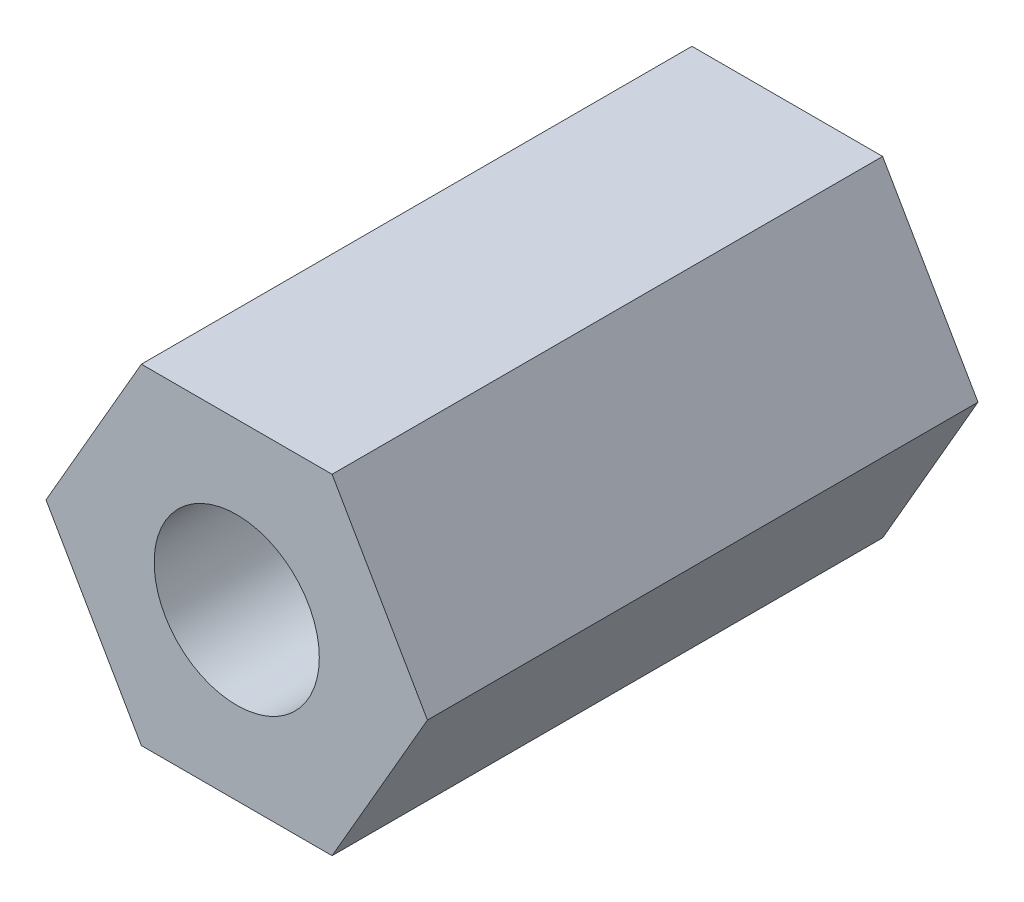
SolidWorks part; units mm, degrees
ref_plane "Plano frontal" through (0, 0, 0) normal (0, 0, 1) x (1, 0, 0)
ref_plane "Plano superior" through (0, 0, 0) normal (0, 1, 0) x (1, 0, 0)
ref_plane "Plano direito" through (0, 0, 0) normal (1, 0, 0) x (0, 0, -1)
sketch "Esboço1" plane through (0, 0, 0) normal (0, 0, 1) x (1, 0, 0)
  line L1 (3.4641, 0) -> (1.7321, 3)
  line L2 (1.7321, 3) -> (-1.7321, 3)
  line L3 (-1.7321, 3) -> (-3.4641, 0)
  line L4 (-3.4641, 0) -> (-1.7321, -3)
  line L5 (-1.7321, -3) -> (1.7321, -3)
  line L6 (1.7321, -3) -> (3.4641, 0)
  circle A0 centre (0, 0) radius 1.5
  circle A1 centre (0, 0) radius 3 construction
  dimension "D1" = 3
extrude "Ressalto-extrusão1" add sketch "Esboço1" along normal blind 10
